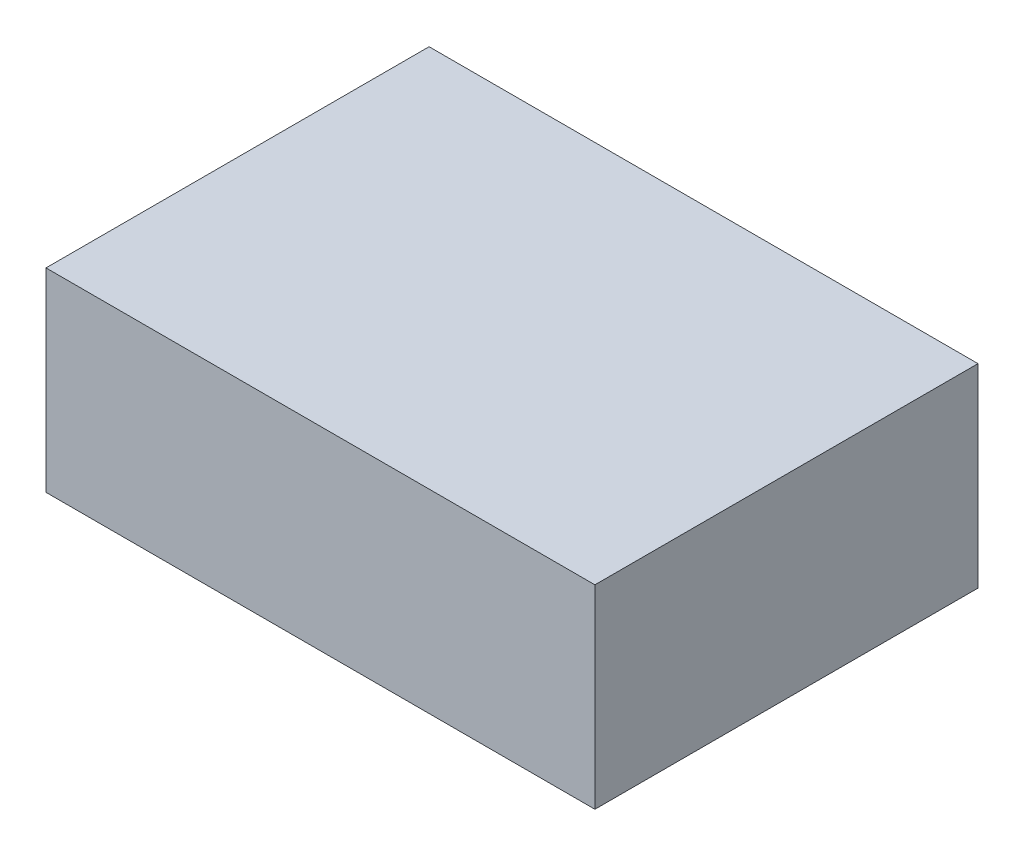
SolidWorks part; units mm, degrees
material "PE Low Density Film"
ref_plane "Front Plane" through (0, 0, 0) normal (0, 0, 1) x (1, 0, 0)
ref_plane "Top Plane" through (0, 0, 0) normal (0, 1, 0) x (1, 0, 0)
ref_plane "Right Plane" through (0, 0, 0) normal (1, 0, 0) x (0, 0, -1)
sketch "Sketch2" plane through (0, 0, 0) normal (0, 1, 0) x (1, 0, 0)
  line L1 (-48, -33.5) -> (48, -33.5)
  line L2 (-48, -33.5) -> (-48, 33.5)
  line L3 (-48, 33.5) -> (48, 33.5)
  line L4 (48, -33.5) -> (48, 33.5)
  line L5 (-48, -33.5) -> (48, 33.5) construction
  line L6 (-48, 33.5) -> (48, -33.5) construction
  point P0 (0, 0)
  dimension "D1" = 96
  dimension "D2" = 67
extrude "Boss-Extrude1" add sketch "Sketch2" along normal blind 34
